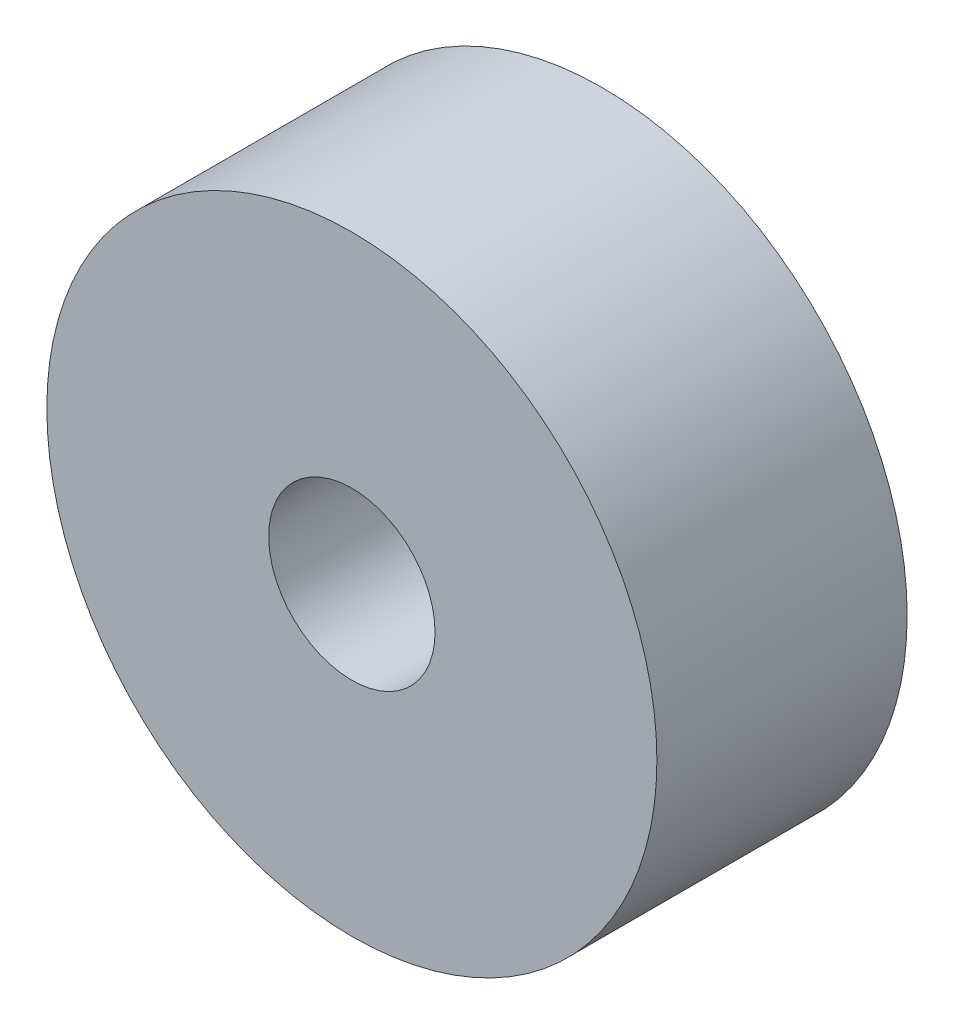
SolidWorks part; units mm, degrees
material "AISI 1020"
ref_plane "Спереди" through (0, 0, 0) normal (0, 0, 1) x (1, 0, 0)
ref_plane "Сверху" through (0, 0, 0) normal (0, 1, 0) x (1, 0, 0)
ref_plane "Справа" through (0, 0, 0) normal (1, 0, 0) x (0, 0, -1)
sketch "Эскиз1" plane through (0, 0, 0) normal (0, 0, 1) x (1, 0, 0)
  circle A0 centre (0, 0) radius 7.9 construction
  circle A1 centre (0, 0) radius 7.9
  circle A2 centre (0, 0) radius 22
  arc A3 (21.3772, 5.1978) -> (-21.3772, 5.1978) centre (0, 0) ccw construction
  dimension "D1" = 44
extrude "Бобышка-Вытянуть1" add sketch "Эскиз1" along normal up to surface (9.05 mm away)
sketch "Эскиз2" plane through (0, 0, 9.05) normal (0, 0, 1) x (1, 0, 0)
  circle A0 centre (-0.0002, 0.0002) radius 6 construction
  circle A1 centre (-0.0002, 0.0002) radius 6
  circle A2 centre (0, 0) radius 22 construction
  circle A3 centre (0, 0) radius 22
extrude "Бобышка-Вытянуть2" add sketch "Эскиз2" along normal offset from surface (9 mm away) 1
